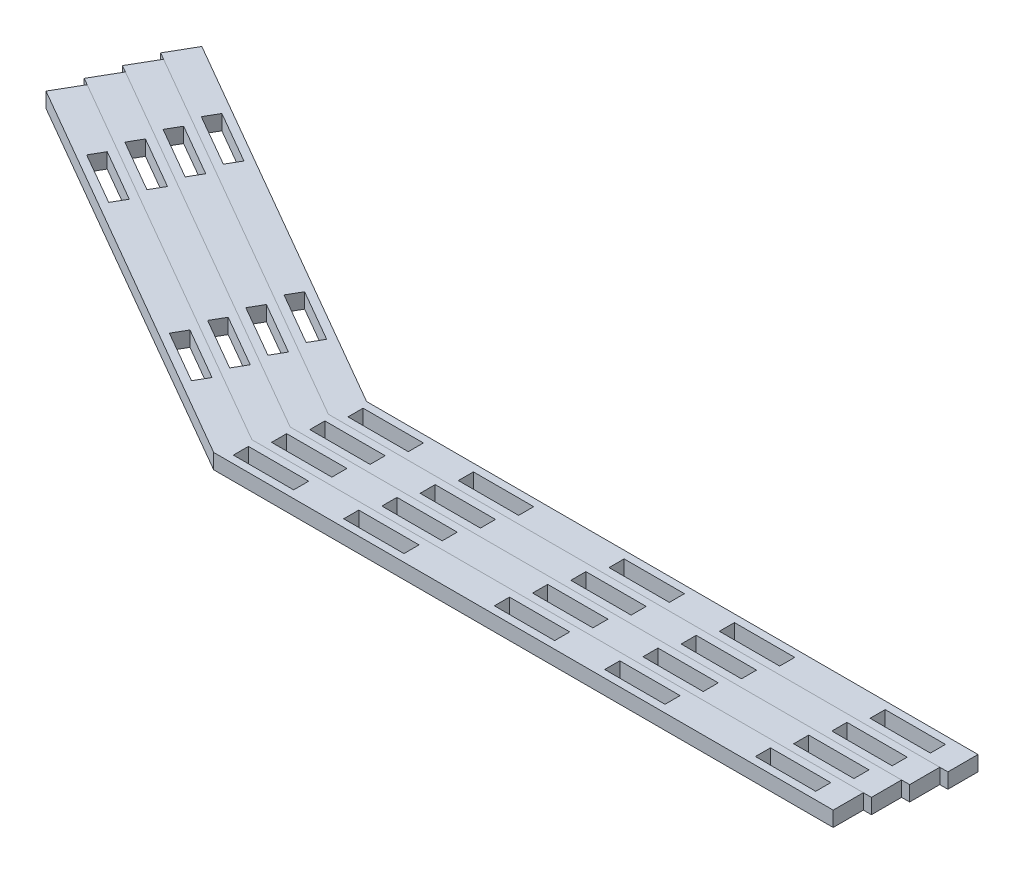
SolidWorks part; units mm, degrees
material "Cedar"
ref_plane "Front Plane" through (0, 0, 0) normal (0, 0, 1) x (1, 0, 0)
ref_plane "Top Plane" through (0, 0, 0) normal (0, 1, 0) x (1, 0, 0)
ref_plane "Right Plane" through (0, 0, 0) normal (1, 0, 0) x (0, 0, -1)
sketch "Sketch4" plane through (0, 0, 0) normal (0, 1, 0) x (1, 0, 0)
  line L0 (-428.2056, 90.1761) -> (-421.8556, 101.1746)
  line L1 (-421.8556, 101.1746) -> (-257.6145, 6.35)
  line L2 (-428.2056, 90.1761) -> (-261.0175, -6.35)
  line L3 (0, -6.35) -> (0, 6.35)
  line L4 (0, 6.35) -> (-257.6145, 6.35)
  line L5 (0, -6.35) -> (-261.0175, -6.35)
  line L6 (-396.3722, 75.4632) -> (-374.3751, 62.7632)
  line L7 (-374.3751, 62.7632) -> (-371.2001, 68.2625)
  line L8 (-371.2001, 68.2625) -> (-393.1972, 80.9625)
  line L9 (-393.1972, 80.9625) -> (-396.3722, 75.4632)
  line L10 (-313.8833, 27.8382) -> (-291.8862, 15.1382)
  line L11 (-291.8862, 15.1382) -> (-288.7112, 20.6375)
  line L12 (-288.7112, 20.6375) -> (-310.7083, 33.3375)
  line L13 (-310.7083, 33.3375) -> (-313.8833, 27.8382)
  line L14 (-255.9131, 3.175) -> (-255.9131, -3.175)
  line L15 (-255.9131, -3.175) -> (-230.5131, -3.175)
  line L16 (-230.5131, -3.175) -> (-230.5131, 3.175)
  line L17 (-230.5131, 3.175) -> (-255.9131, 3.175)
  line L18 (-209.4278, 3.175) -> (-209.4278, -3.175)
  line L19 (-209.4278, -3.175) -> (-184.0278, -3.175)
  line L20 (-184.0278, -3.175) -> (-184.0278, 3.175)
  line L21 (-184.0278, 3.175) -> (-209.4278, 3.175)
  line L22 (-120.5278, -3.175) -> (-120.5278, 3.175)
  line L23 (-120.5278, 3.175) -> (-145.9278, 3.175)
  line L24 (-145.9278, 3.175) -> (-145.9278, -3.175)
  line L25 (-145.9278, -3.175) -> (-120.5278, -3.175)
  line L26 (-99.4426, 3.175) -> (-99.4426, -3.175)
  line L27 (-99.4426, -3.175) -> (-74.0426, -3.175)
  line L28 (-74.0426, -3.175) -> (-74.0426, 3.175)
  line L29 (-74.0426, 3.175) -> (-99.4426, 3.175)
  line L30 (-10.5426, -3.175) -> (-10.5426, 3.175)
  line L31 (-10.5426, 3.175) -> (-35.9426, 3.175)
  line L32 (-35.9426, 3.175) -> (-35.9426, -3.175)
  line L33 (-35.9426, -3.175) -> (-10.5426, -3.175)
  point P34 (0, 0)
  dimension "D1" = 12.7
  dimension "D2" = 261.0175
  dimension "D5" = 193.0522
  dimension "D6" = 12.7
  dimension "D7" = 34.925
  dimension "D8" = 6.35
  dimension "D9" = 25.4
  dimension "D10" = 3.175
  dimension "D11" = 25.4
  dimension "D12" = 6.35
  dimension "D13" = 69.85
  dimension "D14" = 25.4
  dimension "D15" = 6.35
  dimension "D16" = 25.4
  dimension "D17" = 6.35
  dimension "D18" = 3.175
  dimension "D19" = 10.5426
  dimension "D20" = 25.4
  dimension "D21" = 6.35
  dimension "D22" = 25.4
  dimension "D23" = 6.35
  dimension "D24" = 3.175
  dimension "D25" = 38.1
  dimension "D26" = 6.35
  dimension "D27" = 25.4
  dimension "D28" = 6.35
  dimension "D29" = 25.4
  dimension "D30" = 3.175
  dimension "D31" = 21.0852
  dimension "D32" = 6.35
  dimension "D33" = 25.4
  dimension "D34" = 6.35
  dimension "D35" = 25.4
  dimension "D36" = 3.175
  dimension "D37" = 38.1
  dimension "D38" = 6.35
  dimension "D39" = 25.4
  dimension "D40" = 6.35
  dimension "D41" = 25.4
  dimension "D42" = 3.175
  dimension "D43" = 21.0852
  dimension "D44" = 6.35
  dimension "D45" = 25.4
  dimension "D46" = 6.35
  dimension "D47" = 25.4
  dimension "D48" = 3.175
  dimension "D49" = 257.6145
  dimension "D50" = 189.6493
extrude "Boss-Extrude2" add sketch "Sketch4" along normal blind 6.35
sketch "Sketch6" plane through (0, 6.35, 0) normal (0, 1, 0) x (1, 0, 0)
  line L0 (-261.0175, -6.35) -> (-257.6145, 6.35) construction
pattern_linear "LPattern1" count 4 spacing 13.148 along (0.2588, 0, -0.9659) of bodies 102
